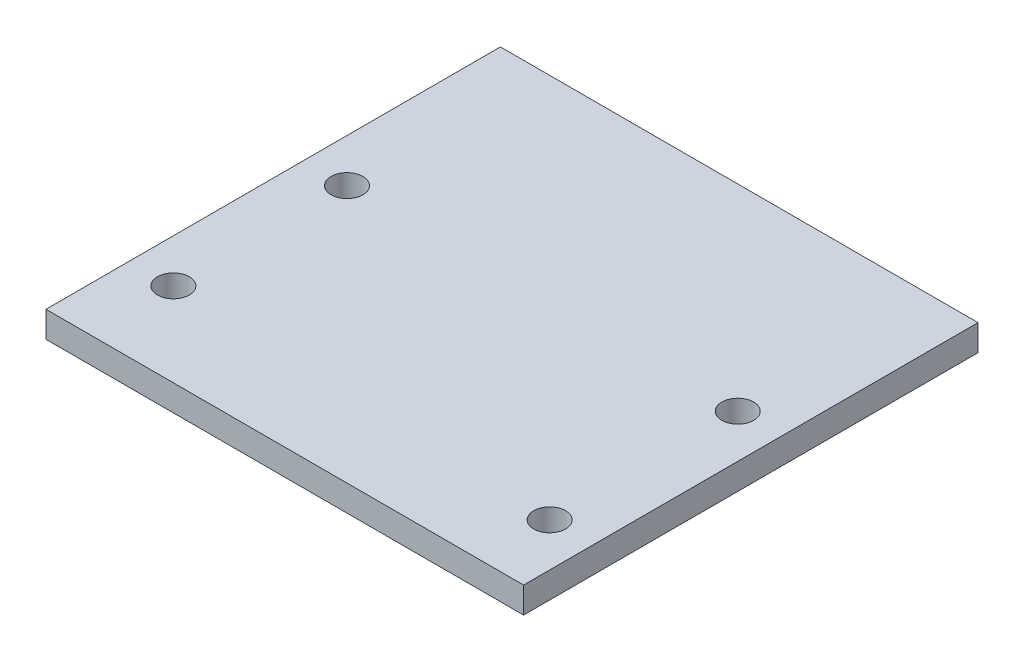
SolidWorks part; units mm, degrees
ref_plane "Front Plane" through (0, 0, 0) normal (0, 0, 1) x (1, 0, 0)
ref_plane "Top Plane" through (0, 0, 0) normal (0, 1, 0) x (1, 0, 0)
ref_plane "Right Plane" through (0, 0, 0) normal (1, 0, 0) x (0, 0, -1)
sketch "Sketch5" plane through (0, 0, 0) normal (0, 1, 0) x (1, 0, 0)
  line L0 (0, 0) -> (-41.91, 0)
  line L1 (-41.91, 0) -> (-41.91, -39.878)
  line L2 (-41.91, -39.878) -> (0, -39.878)
  line L3 (0, -39.878) -> (0, 0)
  line L4 (-41.91, -39.878) -> (-38.1, -39.878) construction
  line L5 (-38.1, -39.878) -> (-38.1, -32.512) construction
  line L6 (-20.955, -39.878) -> (-20.955, 0) construction
  line L7 (-38.1, -39.878) -> (-38.1, -17.272) construction
  line L8 (-3.81, -33.782) -> (-3.81, -39.878) construction
  line L9 (-3.81, -33.782) -> (-3.81, -17.272) construction
  circle A0 centre (-38.1, -17.272) radius 1.397
  circle A1 centre (-38.1, -32.512) radius 1.397
  circle A2 centre (-3.81, -33.782) radius 1.397
  circle A3 centre (-3.81, -17.272) radius 1.397
extrude "Extrude3" add sketch "Sketch5" along normal blind 2.286 separate body
